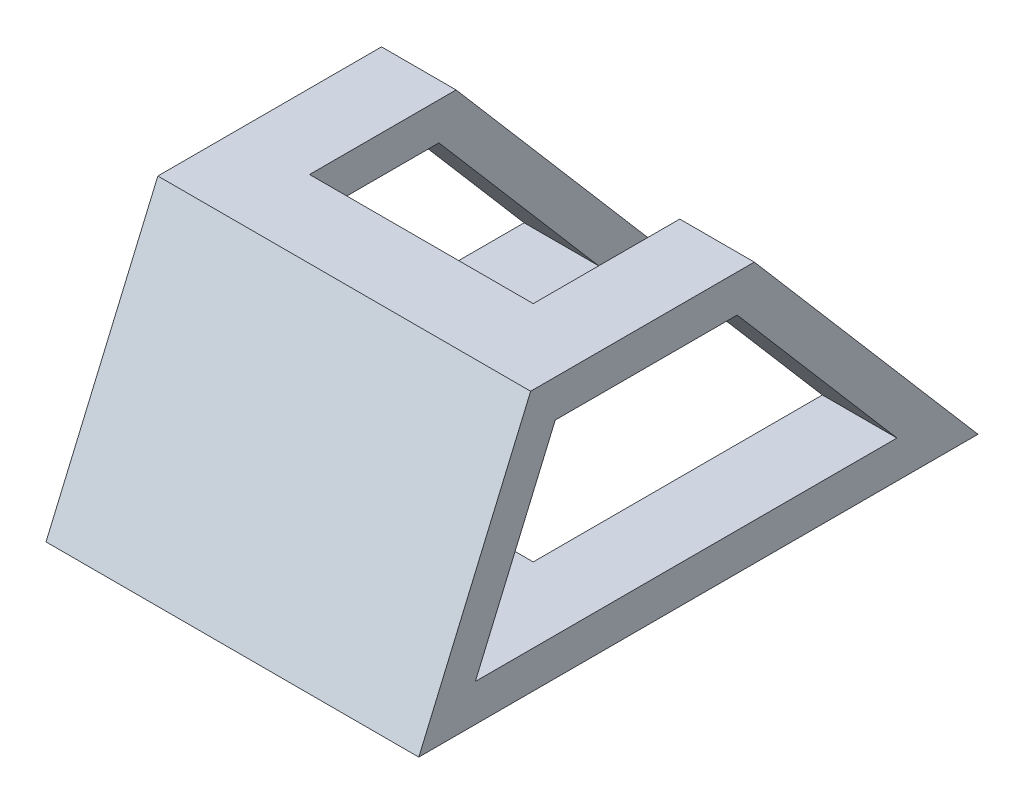
SolidWorks part; units mm, degrees
material "AISI 1020"
ref_plane "Front Plane" through (0, 0, 0) normal (0, 0, 1) x (1, 0, 0)
ref_plane "Top Plane" through (0, 0, 0) normal (0, 1, 0) x (1, 0, 0)
ref_plane "Right Plane" through (0, 0, 0) normal (1, 0, 0) x (0, 0, -1)
sketch "Sketch1" plane through (0, 0, 0) normal (1, 0, 0) x (0, 0, -1)
  line L0 (-75, 0) -> (75, 0)
  line L3 (-75, 0) -> (-45, 70)
  line L4 (-45, 70) -> (15, 70)
  line L5 (15, 70) -> (75, 0)
  line L6 (-38.406, 60) -> (10.4007, 60)
  line L7 (10.4007, 60) -> (53.2578, 10)
  line L8 (-59.8346, 10) -> (53.2578, 10)
  line L9 (-59.8346, 10) -> (-38.406, 60)
  point P4 (0, 0)
  dimension "D1" = 150
  dimension "D2" = 70
  dimension "D3" = 30
  dimension "D4" = 60
  dimension "D5" = 60
  dimension "D6" = 10
extrude "Boss-Extrude1" add sketch "Sketch1" along normal blind 100
sketch "Sketch4" plane through (0, 70, 0) normal (0, 1, 0) x (1, 0, 0)
  line L1 (0, 99.81) -> (100, 99.81)
  line L2 (0, 99.81) -> (0, -45)
  line L3 (0, -45) -> (100, -45)
  line L4 (100, 99.81) -> (100, -45)
  line L5 (20, 75.6972) -> (80, 75.6972)
  line L6 (20, 75.6972) -> (20, -24.3028)
  line L7 (20, -24.3028) -> (80, -24.3028)
  line L8 (80, 75.6972) -> (80, -24.3028)
  dimension "D1" = 20
  dimension "D2" = 60
  dimension "D3" = 100
  dimension "D4" = 20
extrude "Cut-Extrude2" cut sketch "Sketch4" against normal through all contours L6 L5 L8 L7
